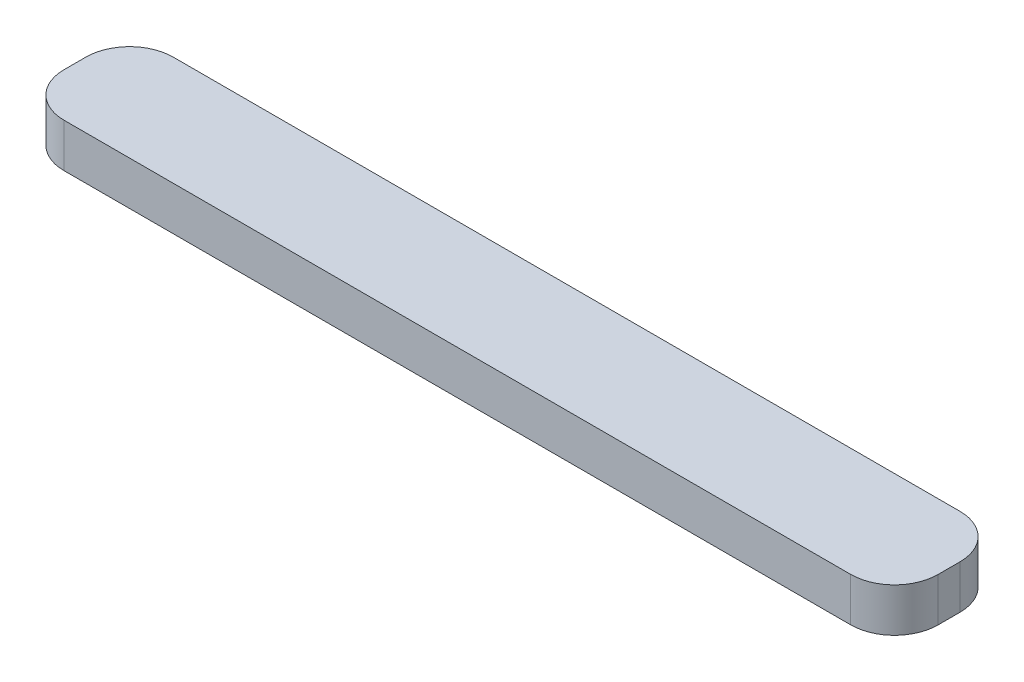
SolidWorks part; units mm, degrees
ref_plane "Ön Düzlem" through (0, 0, 0) normal (0, 0, 1) x (1, 0, 0)
ref_plane "Üst Düzlem" through (0, 0, 0) normal (0, 1, 0) x (1, 0, 0)
ref_plane "Sağ Düzlem" through (0, 0, 0) normal (1, 0, 0) x (0, 0, -1)
sketch "Sketch1" plane through (0, 0, 0) normal (0, 1, 0) x (1, 0, 0)
  line L1 (-18, 2.5) -> (18, 2.5)
  line L2 (-20, 0.5) -> (-20, -0.5)
  line L3 (-18, -2.5) -> (18, -2.5)
  line L4 (20, 0.5) -> (20, -0.5)
  line L5 (-20, 2.5) -> (20, -2.5) construction
  line L6 (-20, -2.5) -> (20, 2.5) construction
  arc A0 (18, -2.5) -> (20, -0.5) centre (18, -0.5) ccw
  arc A1 (18, 2.5) -> (20, 0.5) centre (18, 0.5) cw
  arc A2 (-20, -0.5) -> (-18, -2.5) centre (-18, -0.5) ccw
  arc A3 (-18, 2.5) -> (-20, 0.5) centre (-18, 0.5) ccw
  point P0 (0, 0)
  dimension "D3" = 2
  dimension "D1" = 40
  dimension "D2" = 5
extrude "Boss-Extrude1" add sketch "Sketch1" along normal blind 2
